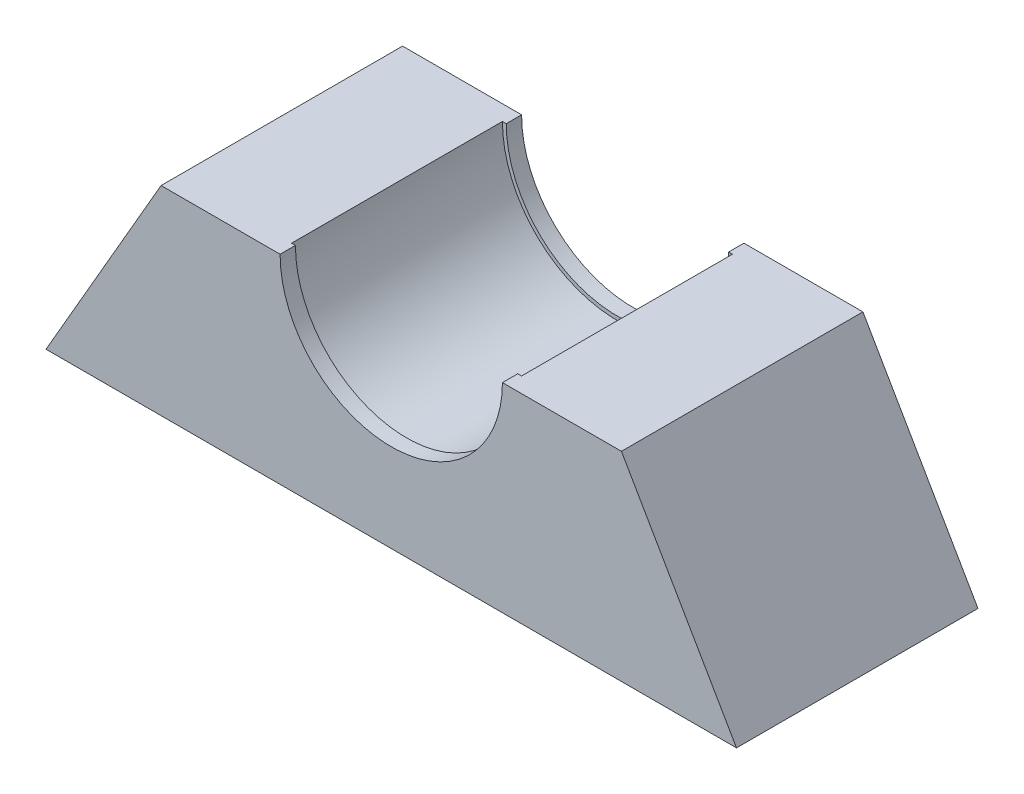
SolidWorks part; units mm, degrees
ref_plane "Front Plane" through (0, 0, 0) normal (0, 0, 1) x (1, 0, 0)
ref_plane "Top Plane" through (0, 0, 0) normal (0, 1, 0) x (1, 0, 0)
ref_plane "Right Plane" through (0, 0, 0) normal (1, 0, 0) x (0, 0, -1)
sketch "Frame" plane through (0, 0, 0) normal (0, 0, 1) x (1, 0, 0)
  line L0 (15, 0) -> (18, 0) construction
  line L1 (0, 0) -> (0, -26) construction
  line L2 (45.0333, -26) -> (0, 52)
  line L3 (0, 52) -> (-45.0333, -26)
  line L4 (-45.0333, -26) -> (45.0333, -26)
  line L5 (0, 0) -> (-30.0222, 0)
  line L6 (0, 0) -> (30.0222, 0)
  circle A0 centre (0, 0) radius 15
  circle A1 centre (0, 0) radius 18
  dimension "D1" = 30
  dimension "D2" = 3
  dimension "D3" = 26
extrude "Boss-Extrude1" add sketch "Frame" along normal blind 27.5 contours A1 L5 L3 L4 L2 L6 | L5 A1 L6 A0
sketch "lip" plane through (0, 0, 27.5) normal (0, 0, 1) x (1, 0, 0)
  line L0 (-14.5, 0) -> (-30.0222, 0)
  line L1 (-30.0222, 0) -> (-45.0333, -26)
  line L2 (-45.0333, -26) -> (45.0333, -26)
  line L3 (45.0333, -26) -> (30.0222, 0)
  line L4 (30.0222, 0) -> (14.5, 0)
  circle A0 centre (0, 0) radius 14.5
  circle A1 centre (0, 0) radius 15
  line M1 (30.0222, 0) -> (15, 0)
  arc M2 (15, 0) -> (-15, 0) centre (0, 0) cw
  line M3 (-15, 0) -> (-30.0222, 0)
  line M4 (-30.0222, 0) -> (-45.0333, -26)
  line M5 (-45.0333, -26) -> (45.0333, -26)
  line M6 (45.0333, -26) -> (30.0222, 0)
  dimension "D1" = 30
  dimension "D2" = 0.5
extrude "Boss-Extrude2" add sketch "lip" along normal blind 2 contours M6 M1 M2 M3 M4 M5 | A0 L0 L4 M2
sketch "lip2" plane through (0, 0, 0) normal (0, 0, -1) x (-1, 0, 0)
  line L0 (-15, 0) -> (-30.0222, 0)
  line L1 (-30.0222, 0) -> (-45.0333, -26)
  line L2 (-45.0333, -26) -> (-30.0222, 0) construction
  line L3 (45.0333, -26) -> (-45.0333, -26) construction
  line L4 (-45.0333, -26) -> (45.0333, -26)
  line L5 (45.0333, -26) -> (30.0222, 0)
  line L6 (30.0222, 0) -> (15, 0)
  line L7 (-15, 0) -> (-14.5, 0)
  line L8 (15, 0) -> (14.5, 0)
  circle A0 centre (0, 0) radius 15
  circle A1 centre (0, 0) radius 14.5
  line M1 (-15, 0) -> (-30.0222, 0)
  line M2 (-30.0222, 0) -> (-45.0333, -26)
  line M3 (-45.0333, -26) -> (45.0333, -26)
  line M4 (45.0333, -26) -> (30.0222, 0)
  line M5 (30.0222, 0) -> (15, 0)
  arc M6 (15, 0) -> (-15, 0) centre (0, 0) cw
  dimension "D1" = 30
  dimension "D2" = 0.5
extrude "Boss-Extrude3" add sketch "lip2" along normal blind 2 contours M6 M1 M2 M3 M4 M5 | A1 L7 L8 M6
